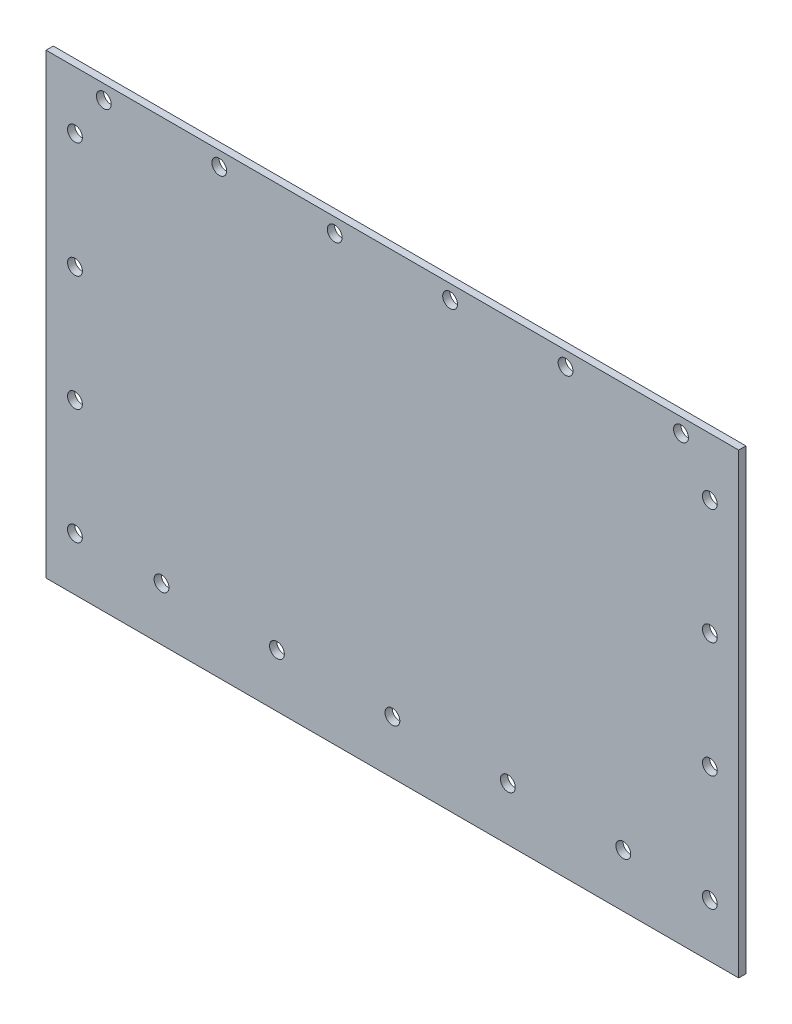
SolidWorks part; units mm, degrees
material "Copper"
ref_plane "Front Plane" through (0, 0, 0) normal (0, 0, 1) x (1, 0, 0)
ref_plane "Top Plane" through (0, 0, 0) normal (0, 1, 0) x (1, 0, 0)
ref_plane "Right Plane" through (0, 0, 0) normal (1, 0, 0) x (0, 0, -1)
sketch "Sketch1" plane through (0, 0, 0) normal (0, 0, 1) x (1, 0, 0)
  line L0 (0, -100.6) -> (152.4, -100.6)
  line L1 (0, 0) -> (152.4, 0)
  line L2 (0, 0) -> (0, -273.05)
  line L3 (0, -273.05) -> (152.4, -273.05)
  line L4 (152.4, 0) -> (152.4, -273.05)
  line L5 (0, -101.6) -> (152.4, -101.6)
  circle A0 centre (6.35, -12.7) radius 1.632
  circle A1 centre (146.05, -12.7) radius 1.632
  circle A2 centre (146.05, -38.1) radius 1.632
  circle A3 centre (146.05, -63.5) radius 1.632
  circle A4 centre (146.05, -88.9) radius 1.632
  circle A5 centre (146.05, -114.3) radius 1.632
  circle A6 centre (146.05, -139.7) radius 1.632
  circle A7 centre (146.05, -165.1) radius 1.632
  circle A8 centre (146.05, -190.5) radius 1.632
  circle A9 centre (146.05, -215.9) radius 1.632
  circle A10 centre (146.05, -241.3) radius 1.632
  circle A11 centre (6.35, -38.1) radius 1.6319
  circle A12 centre (6.35, -63.5) radius 1.6319
  circle A13 centre (6.35, -88.9) radius 1.6319
  circle A14 centre (6.35, -114.3) radius 1.6319
  circle A15 centre (6.35, -139.7) radius 1.632
  circle A16 centre (6.35, -165.1) radius 1.632
  circle A17 centre (6.35, -190.5) radius 1.632
  circle A18 centre (6.35, -215.9) radius 1.632
  circle A19 centre (6.35, -241.3) radius 1.632
  circle A20 centre (12.7, -3.175) radius 1.632
  circle A21 centre (38.1, -3.175) radius 1.632
  circle A22 centre (63.5, -3.175) radius 1.632
  circle A23 centre (88.9, -3.175) radius 1.632
  circle A24 centre (114.3, -3.175) radius 1.632
  circle A25 centre (139.7, -3.175) radius 1.632
  circle A26 centre (25.4, -266.7) radius 1.632
  circle A27 centre (50.8, -266.7) radius 1.632
  circle A28 centre (76.2, -266.7) radius 1.632
  circle A29 centre (101.6, -266.7) radius 1.632
  circle A30 centre (127, -266.7) radius 1.632
  circle A31 centre (25.4, -88.9) radius 1.6319
  circle A32 centre (25.4, -114.3) radius 1.6319
  circle A33 centre (50.8, -114.3) radius 1.6319
  circle A34 centre (50.8, -88.9) radius 1.6319
  circle A35 centre (76.2, -114.3) radius 1.632
  circle A36 centre (76.2, -88.9) radius 1.632
  circle A37 centre (101.6, -114.3) radius 1.632
  circle A38 centre (101.6, -88.9) radius 1.632
  circle A39 centre (127, -114.3) radius 1.632
  circle A40 centre (127, -88.9) radius 1.632
  point P4 (5.4174, -0.218)
  dimension "D3" = 3.2639
  dimension "D1" = 273.05
  dimension "D2" = 152.4
  dimension "D4" = 12.7
  dimension "D5" = 6.35
  dimension "D8" = 6.35
  dimension "D9" = 25.4
  dimension "D10" = 3.175
  dimension "D11" = 12.7
  dimension "D13" = 25.4
  dimension "D14" = 6.35
  dimension "D15" = 25.4
  dimension "D17" = 25.4
  dimension "D18" = 11.7
  dimension "D19" = 1
  dimension "D20" = 25.4
  dimension "D22" = 25.4
  dimension "D23" = 25.4
  dimension "D6" = 2
  dimension "D7" = 10
  dimension "D12" = 6
  dimension "D16" = 5
  dimension "D21" = 5
extrude "Boss-Extrude1" add sketch "Sketch1" along normal blind 1.5875 contours L4 L1 L2 L0 A40 A38 A36 A34 A31 A25 A24 A23 A22 A21 A20 A13 A12 A11 A4 A3 A2 A1 A0
